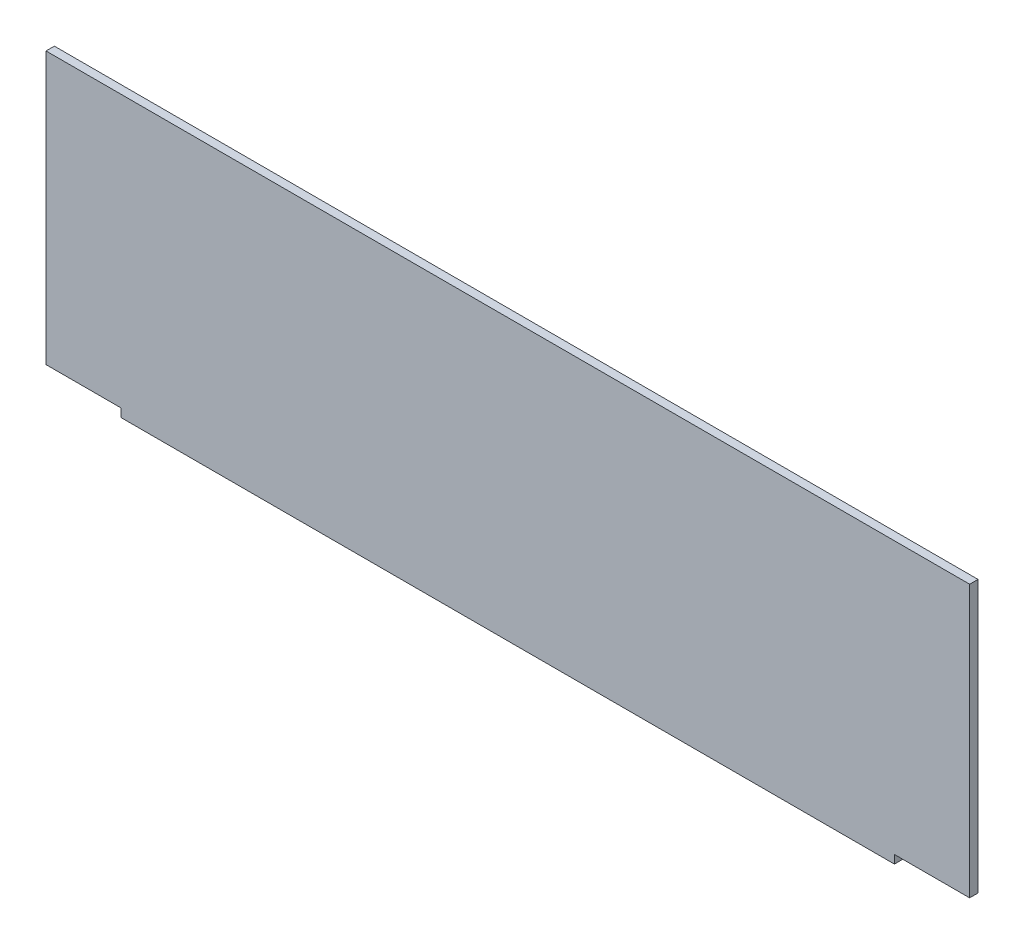
SolidWorks part; units mm, degrees
ref_plane "前视基准面" through (0, 0, 0) normal (0, 0, 1) x (1, 0, 0)
ref_plane "上视基准面" through (0, 0, 0) normal (0, 1, 0) x (1, 0, 0)
ref_plane "右视基准面" through (0, 0, 0) normal (1, 0, 0) x (0, 0, -1)
sketch "草图1" plane through (0, 0, 0) normal (0, 0, 1) x (1, 0, 0)
  line L1 (-92.5, -33.5) -> (92.5, -33.5)
  line L2 (-110.5, -31.5) -> (-110.5, 33.5)
  line L3 (-110.5, 33.5) -> (110.5, 33.5)
  line L4 (110.5, -31.5) -> (110.5, 33.5)
  line L9 (110.5, -31.5) -> (92.5, -31.5)
  line L10 (92.5, -33.5) -> (92.5, -31.5)
  line L13 (-110.5, -31.5) -> (-92.5, -31.5)
  line L14 (-92.5, -33.5) -> (-92.5, -31.5)
  point P0 (0, 0)
  dimension "D1" = 18
  dimension "D2" = 221
  dimension "D3" = 18
  dimension "D4" = 2
  dimension "D5" = 2
  dimension "D6" = 110.5
  dimension "D7" = 65
extrude "凸台-拉伸1" add sketch "草图1" along normal blind 2
